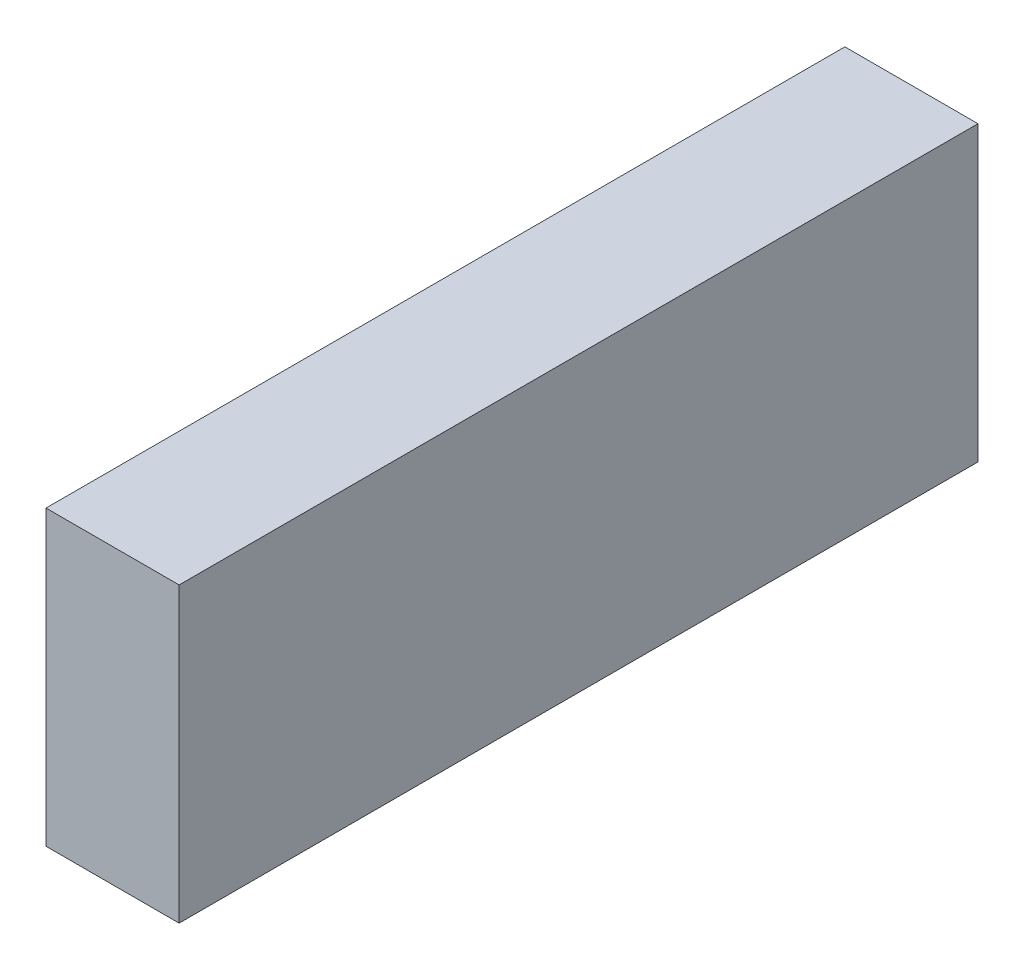
SolidWorks part; units mm, degrees
material "Acrylic (Medium-high impact)"
ref_plane "Front" through (0, 0, 0) normal (0, 0, 1) x (1, 0, 0)
ref_plane "Top" through (0, 0, 0) normal (0, 1, 0) x (1, 0, 0)
ref_plane "Right" through (0, 0, 0) normal (1, 0, 0) x (0, 0, -1)
sketch "Sketch1" plane through (0, 0, 0) normal (1, 0, 0) x (0, 0, -1)
  line L1 (-19.05, 6.985) -> (19.05, 6.985)
  line L2 (-19.05, 6.985) -> (-19.05, -6.985)
  line L3 (-19.05, -6.985) -> (19.05, -6.985)
  line L4 (19.05, 6.985) -> (19.05, -6.985)
  point P5 (0, -6.985)
  point P6 (-19.05, 0)
  dimension "D1" = 38.1
  dimension "D2" = 13.97
extrude "Boss-Extrude1" add sketch "Sketch1" along normal blind 6.35
